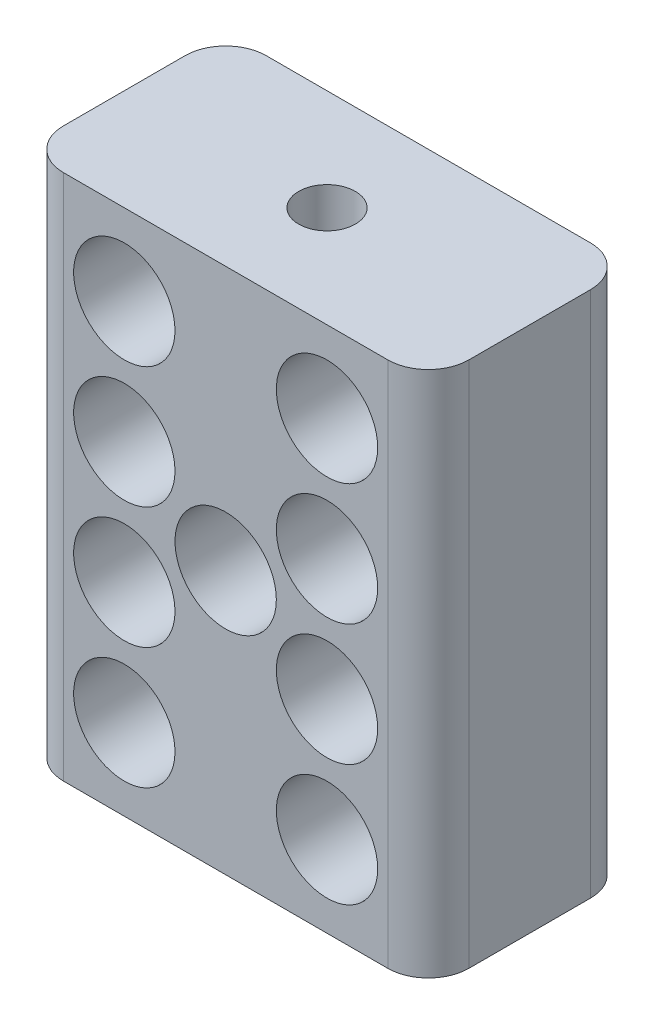
SolidWorks part; units mm, degrees
ref_plane "Front Plane" through (0, 0, 0) normal (0, 0, 1) x (1, 0, 0)
ref_plane "Top Plane" through (0, 0, 0) normal (0, 1, 0) x (1, 0, 0)
ref_plane "Right Plane" through (0, 0, 0) normal (1, 0, 0) x (0, 0, -1)
sketch "Sketch2" plane through (0, 0, 0) normal (0, 0, 1) x (1, 0, 0)
  line L0 (0, 6.5) -> (0, -6.5) construction
  line L1 (-5, 6.5) -> (5, 6.5)
  line L2 (-5, 6.5) -> (-5, -6.5)
  line L3 (-5, -6.5) -> (5, -6.5)
  line L4 (5, 6.5) -> (5, -6.5)
  line L5 (-5, 6.5) -> (5, -6.5) construction
  line L6 (-5, -6.5) -> (5, 6.5) construction
  line L7 (-5, 0) -> (5, 0) construction
  circle A1 centre (-2.5, 4.5) radius 1.25
  circle A2 centre (2.5, 4.5) radius 1.25
  circle A3 centre (7.5, 4.5) radius 1.25 construction
  circle A4 centre (12.5, 4.5) radius 1.25 construction
  circle A5 centre (2.5, 1.5) radius 1.25
  circle A6 centre (7.5, 1.5) radius 1.25 construction
  circle A7 centre (12.5, 1.5) radius 1.25 construction
  circle A8 centre (2.5, -1.5) radius 1.25
  circle A9 centre (7.5, -1.5) radius 1.25 construction
  circle A10 centre (12.5, -1.5) radius 1.25 construction
  circle A11 centre (2.5, -4.5) radius 1.25
  circle A12 centre (7.5, -4.5) radius 1.25 construction
  circle A13 centre (12.5, -4.5) radius 1.25 construction
  circle A14 centre (-2.5, 1.5) radius 1.25
  circle A15 centre (-2.5, -1.5) radius 1.25
  circle A16 centre (-2.5, -4.5) radius 1.25
  circle A17 centre (-7.5, 4.5) radius 1.25 construction
  circle A18 centre (-12.5, 4.5) radius 1.25 construction
  circle A19 centre (-7.5, 1.5) radius 1.25 construction
  circle A20 centre (-12.5, 1.5) radius 1.25 construction
  circle A21 centre (-7.5, -1.5) radius 1.25 construction
  circle A22 centre (-12.5, -1.5) radius 1.25 construction
  circle A23 centre (-7.5, -4.5) radius 1.25 construction
  circle A24 centre (-12.5, -4.5) radius 1.25 construction
  circle A25 centre (-2.5, 1.5) radius 1.25 construction
  circle A26 centre (-2.5, -1.5) radius 1.25 construction
  circle A27 centre (-2.5, -4.5) radius 1.25 construction
  circle A28 centre (-2.5, 1.5) radius 1 construction
  circle A29 centre (-2.5, -1.5) radius 1 construction
  circle A30 centre (0, 0) radius 1.25
  point P0 (0, 0)
  dimension "D2" = 1.5
  dimension "D6" = 2.5
  dimension "D3" = 2
  dimension "D4" = 2.5
  dimension "D1" = 13
  dimension "D11" = 10
  dimension "D12" = 5
  dimension "D13" = 5
  dimension "D7" = 4
  dimension "D8" = 4
  dimension "D9" = 3
  dimension "D10" = 4
extrude "Boss-Extrude1" add sketch "Sketch2" along normal blind 5 contours L4 L1 L2 L3 A24 A23 A22 A21 A20 A19 A18 A17 A16 A15 A14 A13 A12 A11 A10 A9 A8 A7 A6 A5 A4 A3 A2
fillet "Fillet1" radius 1 4 edges at (-5, 0, 0) (-5, 0, 5) (5, 0, 5) (5, 0, 0)
sketch "Sketch3" plane through (0, 6.5, 0) normal (0, 1, 0) x (1, 0, 0)
  line L0 (-5, -2.5) -> (5, -2.5) construction
  line L1 (-5, -4) -> (-5, -1) construction
  line L2 (5, -4) -> (5, -1) construction
  line L3 (0, 0) -> (0, -5) construction
  line L4 (-4, -5) -> (4, -5) construction
  circle A0 centre (0, -2.5) radius 0.7
  circle A1 centre (0, -3.7) radius 0.7 construction
  dimension "D1" = 1.4
  dimension "D3" = 1.2
extrude "Cut-Extrude1" cut sketch "Sketch3" against normal blind 3
mirror "Mirror1" about plane through (0, 0, 0) normal (0, 1, 0) of "Cut-Extrude1"
